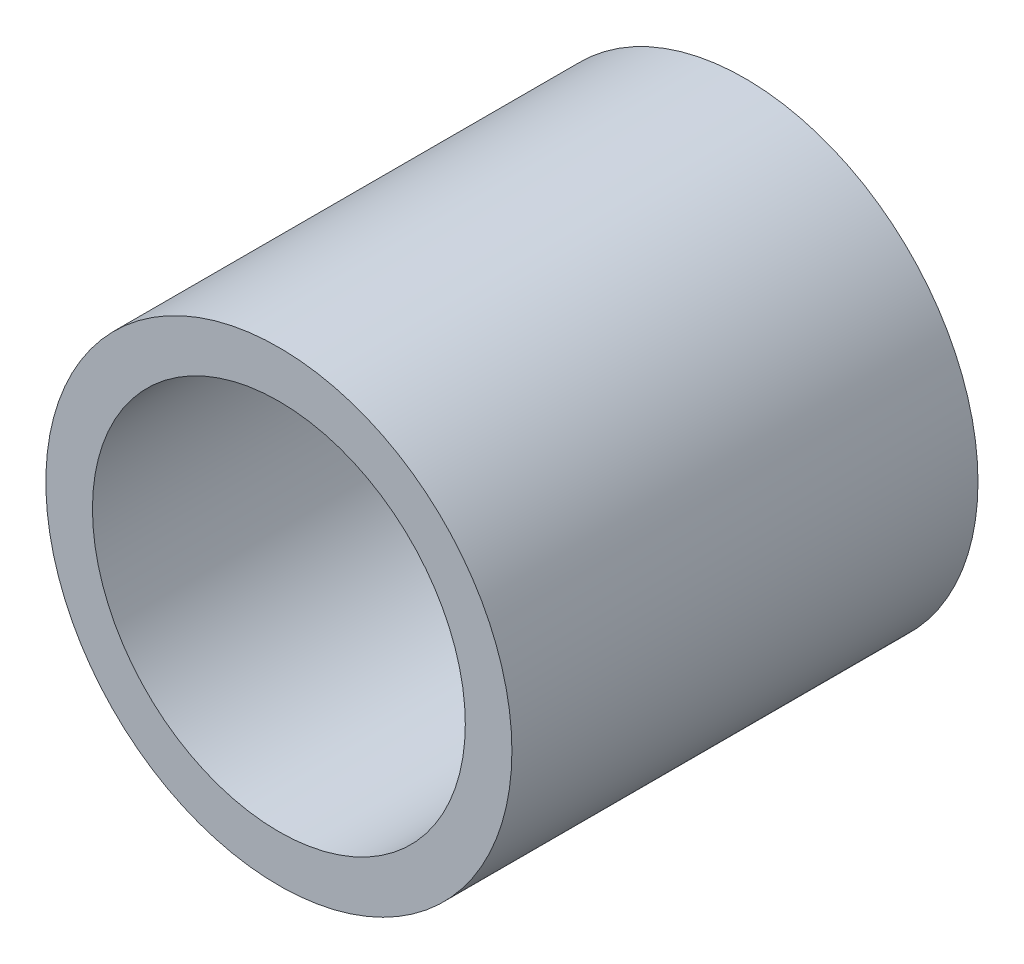
SolidWorks part; units mm, degrees
ref_plane "前视基准面" through (0, 0, 0) normal (0, 0, 1) x (1, 0, 0)
ref_plane "上视基准面" through (0, 0, 0) normal (0, 1, 0) x (1, 0, 0)
ref_plane "右视基准面" through (0, 0, 0) normal (1, 0, 0) x (0, 0, -1)
sketch "草图1" plane through (0, 0, 0) normal (0, 0, 1) x (1, 0, 0)
  circle A0 centre (0, 0) radius 1
  circle A1 centre (0, 0) radius 2
extrude "凸台-拉伸1" add sketch "草图1" along normal blind 1.6
sketch "草图2" plane through (0, 0, 0) normal (0, 0, 1) x (1, 0, 0)
  circle A0 centre (0, 0) radius 2.5
  point P3 (0, 0)
extrude "凸台-拉伸2" add sketch "草图2" along normal blind 5
sketch "草图3" plane through (0, 0, 5) normal (0, 0, 1) x (1, 0, 0)
  circle A0 centre (0, 0) radius 2
extrude "切除-拉伸1" cut sketch "草图3" against normal blind 3.4
sketch "草图4" plane through (0, 0, 1.6) normal (0, 0, 1) x (1, 0, 0)
  circle A0 centre (0, 0) radius 1
extrude "切除-拉伸2" cut sketch "草图4" against normal blind 3.4
